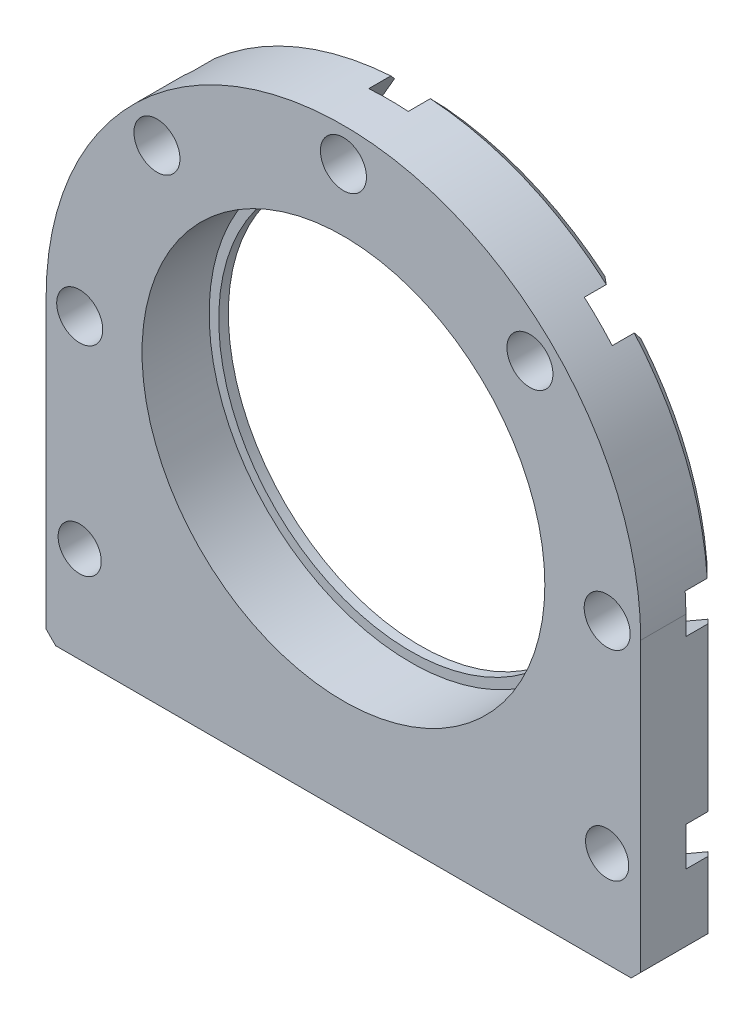
SolidWorks part; units mm, degrees
material "ABS"
ref_plane "正面" through (0, 0, 0) normal (0, 0, 1) x (1, 0, 0)
ref_plane "平面" through (0, 0, 0) normal (0, 1, 0) x (1, 0, 0)
ref_plane "右側面" through (0, 0, 0) normal (1, 0, 0) x (0, 0, -1)
sketch "ｽｹｯﾁ1" plane through (0, 0, 0) normal (0, 0, 1) x (1, 0, 0)
  line L0 (0, 0) -> (0, -31) construction
  line L1 (31, -31) -> (-31, -31)
  line L2 (-31, 0) -> (-31, -31)
  line L3 (31, 0) -> (31, -31)
  circle A0 centre (0, 0) radius 31 construction
  arc A1 (-31, 0) -> (31, 0) centre (0, 0) cw
  point P8 (0, -31)
  dimension "D1" = 62
extrude "ﾎﾞｽ - 押し出し1" add sketch "ｽｹｯﾁ1" along normal blind 8
sketch "ｽｹｯﾁ2" plane through (0, 0, 8) normal (0, 0, 1) x (1, 0, 0)
  circle A0 centre (0, 0) radius 24
  dimension "D1" = 48
extrude "ｶｯﾄ - 押し出し1" [suppressed] cut sketch "ｽｹｯﾁ2" against normal through all
hole_wizard "M4 すきま穴1" positions "ｽｹｯﾁ3" profile "ｽｹｯﾁ4" hole size "M4" standard "JIS" end condition through all
sketch "ｽｹｯﾁ3" plane through (0, 0, 0) normal (0, 0, 1) x (1, 0, 0)
  point P0 (0, 27.5)
  dimension "D1" = 27.5
sketch "ｽｹｯﾁ4" plane through (0, 27.5, 0) normal (1, 0, 0) x (0, 1, 0)
  line L0 (0, 0) -> (0, 8)
  line L1 (0, 8) -> (2.4, 8)
  line L2 (2.4, 8) -> (2.4, 0)
  line L5 (2.4, 0) -> (0, 0)
  line L11 (0, -6.35) -> (0, 107.95) construction
  dimension "通し穴の直径" = 4.8
  dimension "通し穴の深さ" = 8
pattern_circular "円形ﾊﾟﾀｰﾝ1" count 8 over 360 about axis through (0, 0, 0) along (0, 0, 1) skipping 3, 4, 5 of "M4 すきま穴1"
chamfer "面取り1" distance 1 angle 45 6 edges at (31, -31, 4) (-31, -31, 4) (31, -15.5, 0) (0, -31, 0) (-31, -15.5, 0) (0, 31, 0)
sketch "ｽｹｯﾁ5" plane through (0, 0, 0) normal (0, 0, -1) x (-1, 0, 0)
  line L1 (2.0207, 24) -> (4.0415, 27.5)
  line L2 (4.0415, 27.5) -> (2.0207, 31)
  line L3 (2.0207, 31) -> (-2.0207, 31)
  line L4 (-2.0207, 31) -> (-4.0415, 27.5)
  line L5 (-4.0415, 27.5) -> (-2.0207, 24)
  line L6 (-2.0207, 24) -> (2.0207, 24)
  circle A0 centre (0, 27.5) radius 3.5 construction
  dimension "D1" = 7
extrude "ｶｯﾄ - 押し出し2" cut sketch "ｽｹｯﾁ5" against normal blind 3.3
sketch "ｽｹｯﾁ6" plane through (0, 0, 0) normal (0, 0, -1) x (-1, 0, 0)
  circle A0 centre (-2.0207, 24) radius 0.5
  dimension "D1" = 1
extrude "ｶｯﾄ - 押し出し3" [suppressed] cut sketch "ｽｹｯﾁ6" against normal blind 2.6
pattern_circular "円形ﾊﾟﾀｰﾝ2" [suppressed] count 6 over 360
pattern_circular "円形ﾊﾟﾀｰﾝ3" count 8 over 360 about axis through (0, 0, 0) along (0, 0, 1) skipping 3, 4, 5 of "円形ﾊﾟﾀｰﾝ2", "ｶｯﾄ - 押し出し2"
sketch "ｽｹｯﾁ7" plane through (0, 0, 8) normal (0, 0, 1) x (1, 0, 0)
  circle A0 centre (0, 0) radius 21
  dimension "D1" = 42
extrude "ｶｯﾄ - 押し出し4" cut sketch "ｽｹｯﾁ7" against normal blind 7
sketch "ｽｹｯﾁ8" plane through (0, 0, 1) normal (0, 0, 1) x (1, 0, 0)
  circle A0 centre (0, 0) radius 20
  dimension "D1" = 40
extrude "ｶｯﾄ - 押し出し5" cut sketch "ｽｹｯﾁ8" against normal through all
hole_wizard "M4 すきま穴2" positions "ｽｹｯﾁ9" profile "ｽｹｯﾁ10" hole size "M4" standard "JIS" end condition through all
sketch "ｽｹｯﾁ9" plane through (0, 0, 0) normal (0, 0, -1) x (-1, 0, 0)
  line L2 (0, 0) -> (0, -31) construction
  line L3 (30, -31) -> (-30, -31) construction
  line L6 (-27.5, -21) -> (27.5, -21) construction
  point P0 (-27.5, -21)
  point P2 (27.5, -21)
  point P21 (0, 0)
  dimension "D1" = 55
  dimension "D2" = 10
sketch "ｽｹｯﾁ10" plane through (27.5, -21, 0) normal (1, 0, 0) x (0, 1, 0)
  line L0 (0, 0) -> (0, 8)
  line L1 (0, 8) -> (2.25, 8)
  line L2 (2.25, 8) -> (2.25, 0)
  line L5 (2.25, 0) -> (0, 0)
  line L11 (0, -6.35) -> (0, 107.95) construction
  dimension "通し穴の直径" = 4.5
  dimension "通し穴の深さ" = 8
sketch "ｽｹｯﾁ11" plane through (0, 0, 0) normal (0, 0, -1) x (-1, 0, 0)
  line L1 (-24, -23.0207) -> (-24, -18.9793)
  line L2 (-24, -18.9793) -> (-27.5, -16.9585)
  line L3 (-27.5, -16.9585) -> (-31, -18.9793)
  line L4 (-31, -18.9793) -> (-31, -23.0207)
  line L5 (-31, -23.0207) -> (-27.5, -25.0415)
  line L6 (-27.5, -25.0415) -> (-24, -23.0207)
  line L7 (27.5, -25.0415) -> (31, -23.0207)
  line L8 (31, -23.0207) -> (31, -18.9793)
  line L9 (31, -18.9793) -> (27.5, -16.9585)
  line L10 (27.5, -16.9585) -> (24, -18.9793)
  line L11 (24, -18.9793) -> (24, -23.0207)
  line L12 (24, -23.0207) -> (27.5, -25.0415)
  circle A0 centre (-27.5, -21) radius 3.5 construction
  circle A1 centre (27.5, -21) radius 3.5 construction
  dimension "D1" = 7
  dimension "D2" = 7
extrude "ｶｯﾄ - 押し出し6" cut sketch "ｽｹｯﾁ11" against normal blind 3.3
